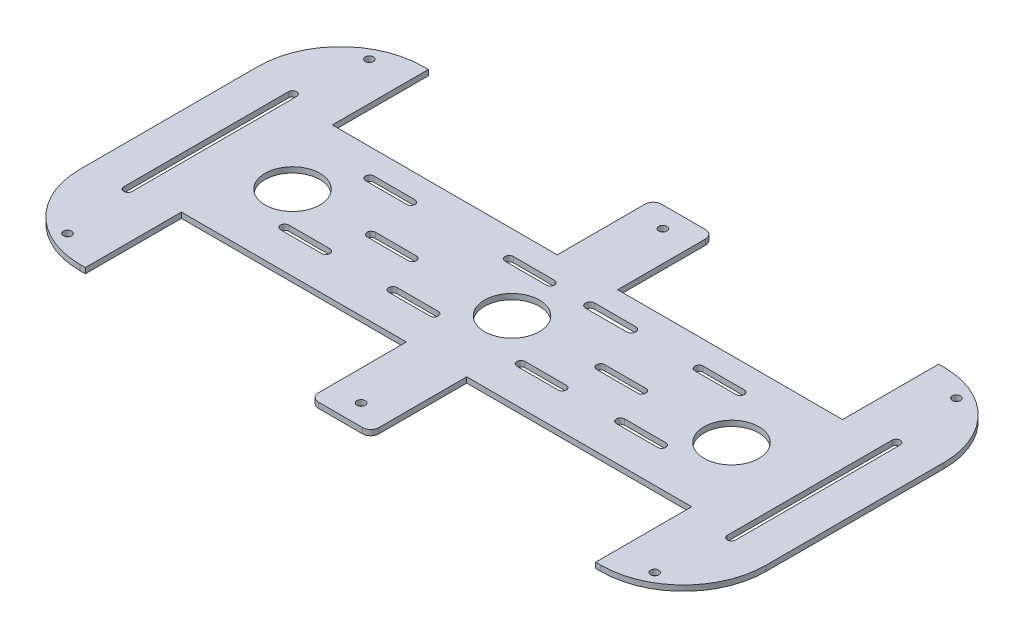
SolidWorks part; units mm, degrees
ref_plane "前视基准面" through (0, 0, 0) normal (0, 0, 1) x (1, 0, 0)
ref_plane "上视基准面" through (0, 0, 0) normal (0, 1, 0) x (1, 0, 0)
ref_plane "右视基准面" through (0, 0, 0) normal (1, 0, 0) x (0, 0, -1)
sketch "草图1" plane through (0, 0, 0) normal (0, 1, 0) x (1, 0, 0)
  line L0 (-110, 30) -> (-110, -30) construction
  line L1 (-95, -62.5) -> (95, -62.5)
  line L2 (-125, -32.5) -> (-125, 32.5)
  line L3 (-95, 62.5) -> (95, 62.5)
  line L4 (125, -32.5) -> (125, 32.5)
  line L5 (-125, -62.5) -> (125, 62.5) construction
  line L6 (-125, 62.5) -> (125, -62.5) construction
  line L7 (-108.5, 30) -> (-108.5, -30)
  line L8 (-111.5, 30) -> (-111.5, -30)
  line L9 (-137.5, 0) -> (137.5, 0) construction
  line L10 (110, 30) -> (110, -30) construction
  line L11 (111.5, 30) -> (111.5, -30)
  line L12 (108.5, 30) -> (108.5, -30)
  line L13 (-51.3025, 0) -> (-36.3025, 0) construction
  line L14 (-51.3025, 1.5) -> (-36.3025, 1.5)
  line L15 (-51.3025, -1.5) -> (-36.3025, -1.5)
  line L16 (-69.3409, 17.4714) -> (-54.3409, 17.4714) construction
  line L17 (-69.3409, 18.9714) -> (-54.3409, 18.9714)
  line L18 (-69.3409, 15.9714) -> (-54.3409, 15.9714)
  line L19 (-18.5, 17.4714) -> (-3.5, 17.4714) construction
  line L20 (-18.5, 18.9714) -> (-3.5, 18.9714)
  line L21 (-18.5, 15.9714) -> (-3.5, 15.9714)
  line L22 (-69.3409, -13.5094) -> (-54.3409, -13.5094) construction
  line L23 (-69.3409, -12.0094) -> (-54.3409, -12.0094)
  line L24 (-69.3409, -15.0094) -> (-54.3409, -15.0094)
  line L25 (-29.8923, -13.5094) -> (-14.8923, -13.5094) construction
  line L26 (-29.8923, -12.0094) -> (-14.8923, -12.0094)
  line L27 (-29.8923, -15.0094) -> (-14.8923, -15.0094)
  line L28 (11, 17.4714) -> (26, 17.4714) construction
  line L29 (11, 19.1214) -> (26, 19.1214)
  line L30 (11, 15.8214) -> (26, 15.8214)
  line L31 (32.315, 0) -> (47.315, 0) construction
  line L32 (32.315, 1.5) -> (47.315, 1.5)
  line L33 (32.315, -1.5) -> (47.315, -1.5)
  line L34 (16.8053, -13.5094) -> (31.8053, -13.5094) construction
  line L35 (16.8053, -12.0094) -> (31.8053, -12.0094)
  line L36 (16.8053, -15.0094) -> (31.8053, -15.0094)
  line L37 (53.0507, -13.5094) -> (68.0507, -13.5094) construction
  line L38 (53.0507, -12.0094) -> (68.0507, -12.0094)
  line L39 (53.0507, -15.0094) -> (68.0507, -15.0094)
  line L40 (50.6906, 17.4714) -> (65.6906, 17.4714) construction
  line L41 (50.6906, 18.9714) -> (65.6906, 18.9714)
  line L42 (50.6906, 15.9714) -> (65.6906, 15.9714)
  line L43 (-11, 62.5) -> (-11, 27.5)
  line L44 (11, 62.5) -> (11, 27.5)
  line L45 (0, -68.75) -> (0, 68.75) construction
  line L46 (-93, 62.5) -> (-93, 27.5)
  line L47 (-93, 27.5) -> (-11, 27.5)
  line L48 (-93, -62.5) -> (-93, -27.5)
  line L49 (-93, -27.5) -> (-11, -27.5)
  line L50 (-11, -27.5) -> (-11, -62.5)
  line L51 (11, -62.5) -> (11, -27.5)
  line L52 (11, -27.5) -> (93, -27.5)
  line L53 (93, -27.5) -> (93, -62.5)
  line L54 (93, 62.5) -> (93, 27.5)
  line L55 (93, 27.5) -> (11, 27.5)
  line L56 (-93, 62.5) -> (-11, 62.5)
  line L57 (11, 62.5) -> (93, 62.5)
  line L58 (93, -62.5) -> (11, -62.5)
  line L59 (-93, -62.5) -> (-11, -62.5)
  arc A0 (95, 62.5) -> (125, 32.5) centre (95, 32.5) cw
  arc A1 (95, -62.5) -> (125, -32.5) centre (95, -32.5) ccw
  arc A2 (-95, -62.5) -> (-125, -32.5) centre (-95, -32.5) cw
  arc A3 (-125, 32.5) -> (-95, 62.5) centre (-95, 32.5) cw
  arc A4 (-108.5, 30) -> (-111.5, 30) centre (-110, 30) ccw
  arc A5 (-111.5, -30) -> (-108.5, -30) centre (-110, -30) ccw
  arc A6 (111.5, 30) -> (108.5, 30) centre (110, 30) ccw
  arc A7 (108.5, -30) -> (111.5, -30) centre (110, -30) ccw
  circle A8 centre (-80, 0) radius 10
  circle A9 centre (0, 0) radius 10
  circle A10 centre (80, 0) radius 10
  arc A11 (-51.3025, 1.5) -> (-51.3025, -1.5) centre (-51.3025, 0) ccw
  arc A12 (-36.3025, -1.5) -> (-36.3025, 1.5) centre (-36.3025, 0) ccw
  arc A13 (-69.3409, 18.9714) -> (-69.3409, 15.9714) centre (-69.3409, 17.4714) ccw
  arc A14 (-54.3409, 15.9714) -> (-54.3409, 18.9714) centre (-54.3409, 17.4714) ccw
  arc A15 (-18.5, 18.9714) -> (-18.5, 15.9714) centre (-18.5, 17.4714) ccw
  arc A16 (-3.5, 15.9714) -> (-3.5, 18.9714) centre (-3.5, 17.4714) ccw
  arc A17 (-69.3409, -12.0094) -> (-69.3409, -15.0094) centre (-69.3409, -13.5094) ccw
  arc A18 (-54.3409, -15.0094) -> (-54.3409, -12.0094) centre (-54.3409, -13.5094) ccw
  arc A19 (-29.8923, -12.0094) -> (-29.8923, -15.0094) centre (-29.8923, -13.5094) ccw
  arc A20 (-14.8923, -15.0094) -> (-14.8923, -12.0094) centre (-14.8923, -13.5094) ccw
  arc A21 (11, 19.1214) -> (11, 15.8214) centre (11, 17.4714) ccw
  arc A22 (26, 15.8214) -> (26, 19.1214) centre (26, 17.4714) ccw
  arc A23 (32.315, 1.5) -> (32.315, -1.5) centre (32.315, 0) ccw
  arc A24 (47.315, -1.5) -> (47.315, 1.5) centre (47.315, 0) ccw
  arc A25 (16.8053, -12.0094) -> (16.8053, -15.0094) centre (16.8053, -13.5094) ccw
  arc A26 (31.8053, -15.0094) -> (31.8053, -12.0094) centre (31.8053, -13.5094) ccw
  arc A27 (53.0507, -12.0094) -> (53.0507, -15.0094) centre (53.0507, -13.5094) ccw
  arc A28 (68.0507, -15.0094) -> (68.0507, -12.0094) centre (68.0507, -13.5094) ccw
  arc A29 (50.6906, 18.9714) -> (50.6906, 15.9714) centre (50.6906, 17.4714) ccw
  arc A30 (65.6906, 15.9714) -> (65.6906, 18.9714) centre (65.6906, 17.4714) ccw
  point P0 (0, 0)
  point P20 (-110, 0)
  point P29 (110, 0)
  point P42 (-43.8025, 0)
  point P47 (-61.8409, 17.4714)
  point P54 (-11, 17.4714)
  point P61 (-61.8409, -13.5094)
  point P68 (-22.3923, -13.5094)
  point P75 (18.5, 17.4714)
  point P82 (39.815, 0)
  point P89 (24.3053, -13.5094)
  point P96 (60.5507, -13.5094)
  point P103 (58.1906, 17.4714)
  dimension "D3" = 30
  dimension "D6" = 1.5
  dimension "D8" = 1.5
  dimension "D12" = 20
  dimension "D13" = 20
  dimension "D14" = 20
  dimension "D17" = 1.5
  dimension "D20" = 1.5
  dimension "D21" = 1.5
  dimension "D24" = 1.5
  dimension "D25" = 1.5
  dimension "D28" = 1.5
  dimension "D29" = 1.5
  dimension "D31" = 1.5
  dimension "D34" = 1.65
  dimension "D35" = 1.5
  dimension "D1" = 250
  dimension "D2" = 125
  dimension "D4" = 60
  dimension "D5" = 30
  dimension "D7" = 15
  dimension "D9" = 60
  dimension "D10" = 30
  dimension "D11" = 15
  dimension "D15" = 80
  dimension "D16" = 80
  dimension "D18" = 15
  dimension "D19" = 15
  dimension "D22" = 15
  dimension "D23" = 15
  dimension "D26" = 15
  dimension "D27" = 15
  dimension "D30" = 15
  dimension "D32" = 15
  dimension "D33" = 15
  dimension "D36" = 15
  dimension "D37" = 35
  dimension "D38" = 22
  dimension "D39" = 11
  dimension "D40" = 35
  dimension "D41" = 32
  dimension "D42" = 32
  dimension "D43" = 35
  dimension "D44" = 35
  dimension "D45" = 22
extrude "凸台-拉伸1" add sketch "草图1" along normal blind 2 contours A3 L2 A2 L1 L48 L49 L50 L51 L52 L53 A1 L4 A0 L3 L54 L55 L44 L43 L47 L46 A30 L42 A29 L41 A28 L39 A27 L38 A26 L36 A25 L35 A24 L33 A23 L32 A22 L30 A21 L29 A20
fillet "圆角1" radius 3 4 edges at (11, 1, 62.5) (-11, 1, 62.5) (11, 1, -62.5) (-11, 1, -62.5)
sketch "草图2" plane through (0, 2, 0) normal (0, 1, 0) x (1, 0, 0)
  line L0 (-1.1, 0) -> (1.1, 0) construction
  line L1 (107, -55) -> (-107, -55) construction
  line L2 (107, -55) -> (107, 55) construction
  line L3 (107, 55) -> (-107, 55) construction
  line L4 (-107, -55) -> (-107, 55) construction
  line L5 (0, -1.1) -> (0, 1.1) construction
  circle A0 centre (107, -55) radius 1.5
  circle A1 centre (107, 55) radius 1.5
  circle A2 centre (-107, 55) radius 1.5
  circle A3 centre (-107, -55) radius 1.5
  dimension "D5" = 3
  dimension "D6" = 3
  dimension "D7" = 3
  dimension "D8" = 3
  dimension "D1" = 110
  dimension "D2" = 55
  dimension "D3" = 214
  dimension "D4" = 107
extrude "切除-拉伸1" cut sketch "草图2" against normal through all
sketch "草图3" plane through (0, 0, 0) normal (0, -1, 0) x (1, 0, 0)
  line L0 (11, 59.5) -> (11, 27.5) construction
  line L1 (11, -59.5) -> (11, -27.5) construction
  circle A0 centre (0, 55) radius 1.5
  circle A1 centre (0, -55) radius 1.5
  dimension "D1" = 3
  dimension "D2" = 3
  dimension "D3" = 110
  dimension "D4" = 55
  dimension "D5" = 11
  dimension "D6" = 11
extrude "切除-拉伸2" cut sketch "草图3" against normal blind 10
